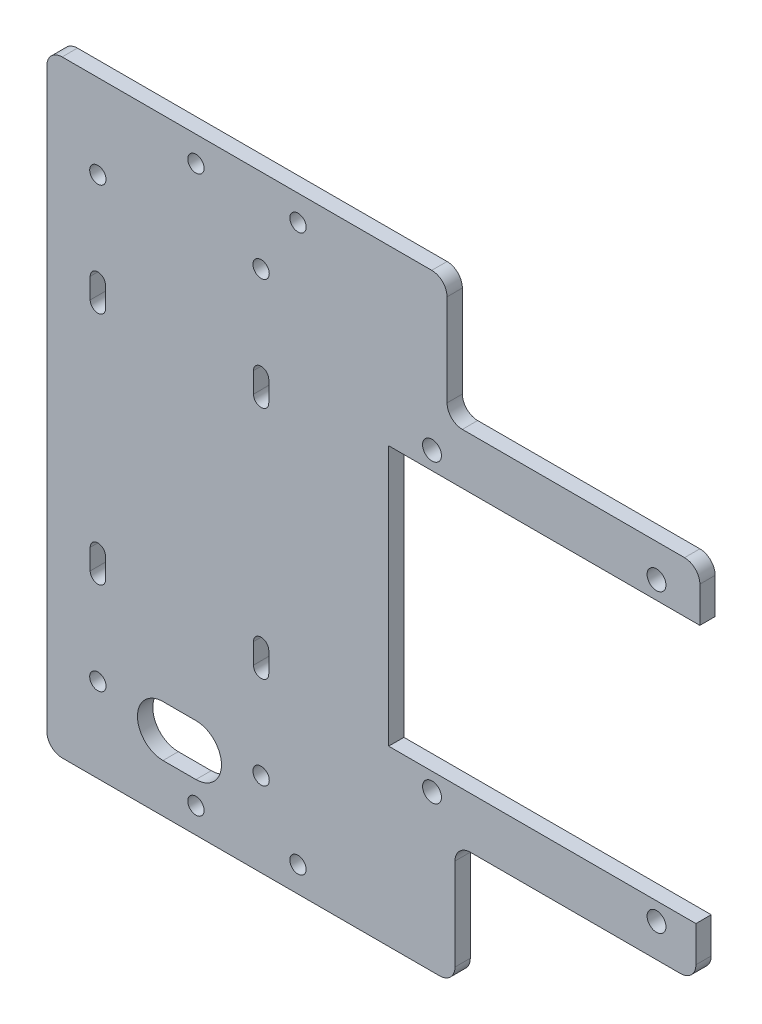
SolidWorks part; units mm, degrees
material "尼龙 101"
ref_plane "前视基准面" through (0, 0, 0) normal (0, 0, 1) x (1, 0, 0)
ref_plane "上视基准面" through (0, 0, 0) normal (0, 1, 0) x (1, 0, 0)
ref_plane "右视基准面" through (0, 0, 0) normal (1, 0, 0) x (0, 0, -1)
other "Configuration Table"
sketch "草图1" plane through (0, 0, 0) normal (0, 0, 1) x (1, 0, 0)
  line L0 (65.7597, 31.4573) -> (53.5352, 31.4573)
  line L1 (15.7597, 60.4573) -> (35.7597, 60.4573) construction
  line L2 (15.7597, 60.4573) -> (15.7597, -48.5427) construction
  line L3 (15.7597, -48.5427) -> (35.7597, -48.5427) construction
  line L4 (35.7597, 60.4573) -> (35.7597, -48.5427) construction
  line L5 (-13.4648, 65.4573) -> (64.9841, 65.4573)
  line L6 (-13.4648, 65.4573) -> (-13.4648, -53.5427)
  line L7 (-13.4648, -53.5427) -> (66.5352, -53.5427)
  line L8 (64.9841, 65.4573) -> (64.9841, 41.4573)
  line L9 (-3.4648, 48.9573) -> (28.5352, 48.9573) construction
  line L10 (-3.4648, 48.9573) -> (-3.4648, -37.0427) construction
  line L11 (-3.4648, -37.0427) -> (28.5352, -37.0427) construction
  line L12 (28.5352, 48.9573) -> (28.5352, -37.0427) construction
  line L25 (62.0352, 34.9573) -> (106.0352, 34.9573) construction
  line L26 (62.0352, 34.9573) -> (62.0352, -23.0427) construction
  line L27 (62.0352, -23.0427) -> (106.0352, -23.0427) construction
  line L28 (106.0352, 34.9573) -> (106.0352, -23.0427) construction
  line L29 (53.5352, 31.4573) -> (114.5352, 31.4573) construction
  line L30 (53.5352, 31.4573) -> (53.5352, -19.5427) construction
  line L31 (53.5352, -19.5427) -> (114.5352, -19.5427) construction
  line L32 (114.5352, 31.4573) -> (114.5352, -19.5427) construction
  line L33 (53.5352, 31.4573) -> (53.5352, -19.5427)
  line L34 (53.5352, -19.5427) -> (64.9841, -19.5427)
  line L37 (114.5352, 31.4573) -> (65.7597, 31.4573)
  line L38 (114.5352, 31.4573) -> (114.5352, 41.4573)
  line L39 (114.5352, 41.4573) -> (64.9841, 41.4573)
  line L41 (64.9841, -19.5427) -> (113.7597, -19.5427)
  line L43 (66.5352, -29.5427) -> (113.7597, -29.5427)
  line L44 (113.7597, -19.5427) -> (113.7597, -29.5427)
  line L45 (66.5352, -29.5427) -> (66.5352, -53.5427)
  line L46 (-3.4648, -37.0427) -> (-3.4648, -56.7871) construction
  line L47 (0.5352, 34.9573) -> (24.5352, 34.9573) construction
  line L48 (0.5352, 34.9573) -> (0.5352, -23.0427) construction
  line L49 (0.5352, -23.0427) -> (24.5352, -23.0427) construction
  line L50 (24.5352, 34.9573) -> (24.5352, -23.0427) construction
  line L51 (9.3027, -39.0925) -> (15.7597, -39.0925) construction
  line L52 (9.3027, -34.0925) -> (15.7597, -34.0925)
  line L53 (9.3027, -44.0925) -> (15.7597, -44.0925)
  line L54 (-3.4648, 30.9573) -> (-3.4648, 26.9573) construction
  line L55 (-1.9648, 30.9573) -> (-1.9648, 26.9573)
  line L56 (-4.9648, 30.9573) -> (-4.9648, 26.9573)
  line L57 (-3.4648, -15.0427) -> (-3.4648, -19.0427) construction
  line L58 (-1.9648, -15.0427) -> (-1.9648, -19.0427)
  line L59 (-4.9648, -15.0427) -> (-4.9648, -19.0427)
  line L60 (12.5352, 34.9573) -> (12.5352, -23.0427) construction
  line L61 (28.5352, -15.0427) -> (28.5352, -19.0427) construction
  line L62 (27.0352, -15.0427) -> (27.0352, -19.0427)
  line L63 (30.0352, -15.0427) -> (30.0352, -19.0427)
  line L64 (28.5352, 30.9573) -> (28.5352, 26.9573) construction
  line L65 (27.0352, 30.9573) -> (27.0352, 26.9573)
  line L66 (30.0352, 30.9573) -> (30.0352, 26.9573)
  circle A0 centre (15.7597, 60.4573) radius 1.6
  circle A1 centre (35.7597, 60.4573) radius 1.6
  circle A2 centre (15.7597, -48.5427) radius 1.6
  circle A3 centre (35.7597, -48.5427) radius 1.6
  circle A4 centre (-3.4648, 48.9573) radius 1.6
  circle A5 centre (28.5352, 48.9573) radius 1.6
  circle A6 centre (-3.4648, -37.0427) radius 1.6
  circle A7 centre (28.5352, -37.0427) radius 1.6
  circle A12 centre (62.0352, -23.0427) radius 1.85
  circle A13 centre (106.0352, -23.0427) radius 1.85
  circle A14 centre (62.0352, 34.9573) radius 1.85
  circle A15 centre (106.0352, 34.9573) radius 1.85
  arc A16 (9.3027, -34.0925) -> (9.3027, -44.0925) centre (9.3027, -39.0925) ccw
  arc A17 (15.7597, -44.0925) -> (15.7597, -34.0925) centre (15.7597, -39.0925) ccw
  arc A18 (-1.9648, 30.9573) -> (-4.9648, 30.9573) centre (-3.4648, 30.9573) ccw
  arc A19 (-4.9648, 26.9573) -> (-1.9648, 26.9573) centre (-3.4648, 26.9573) ccw
  arc A20 (-1.9648, -15.0427) -> (-4.9648, -15.0427) centre (-3.4648, -15.0427) ccw
  arc A21 (-4.9648, -19.0427) -> (-1.9648, -19.0427) centre (-3.4648, -19.0427) ccw
  arc A22 (27.0352, -15.0427) -> (30.0352, -15.0427) centre (28.5352, -15.0427) cw
  arc A23 (30.0352, -19.0427) -> (27.0352, -19.0427) centre (28.5352, -19.0427) cw
  arc A24 (27.0352, 30.9573) -> (30.0352, 30.9573) centre (28.5352, 30.9573) cw
  arc A25 (30.0352, 26.9573) -> (27.0352, 26.9573) centre (28.5352, 26.9573) cw
  point P12 (25.7597, 60.4573)
  point P13 (25.7597, 65.4573)
  point P14 (-13.4648, 5.9573)
  point P15 (15.7597, 5.9573)
  point P20 (28.5352, 5.9573)
  point P29 (0.5352, 5.9573)
  point P33 (12.5312, -39.0925)
  point P38 (12.5352, 34.9573)
  point P39 (12.5352, 48.9573)
  point P41 (35.7597, 5.9573)
  point P43 (-3.4648, 28.9573)
  point P51 (84.0352, 34.9573)
  point P52 (84.0352, 31.4573)
  point P61 (53.5352, 5.9573)
  point P62 (62.0352, 5.9573)
  point P71 (-3.4648, -17.0427)
  point P80 (28.5352, -17.0427)
  point P89 (28.5352, 28.9573)
  dimension "D3" = 3.2
  dimension "D9" = 3.2
  dimension "D15" = 10
  dimension "D19" = 3.7
  dimension "D13" = 20
  dimension "D1" = 109
  dimension "D2" = 20
  dimension "D4" = 5
  dimension "D5" = 5
  dimension "D6" = 80
  dimension "D7" = 86
  dimension "D8" = 32
  dimension "D10" = 10
  dimension "D11" = 24
  dimension "D12" = 58
  dimension "D14" = 20
  dimension "D16" = 10
  dimension "D17" = 44
  dimension "D18" = 58
  dimension "D20" = 61
  dimension "D21" = 51
  dimension "D22" = 25
extrude "凸台-拉伸1" add sketch "草图1" along normal blind 3
fillet "圆角1" radius 3 8 edges at (64.9841, 65.4573, 1.5) (64.9841, 41.4573, 1.5) (114.5352, 41.4573, 1.5) (113.7597, -29.5427, 1.5) (66.5352, -29.5427, 1.5) (66.5352, -53.5427, 1.5) (-13.4648, -53.5427, 1.5) (-13.4648, 65.4573, 1.5)
